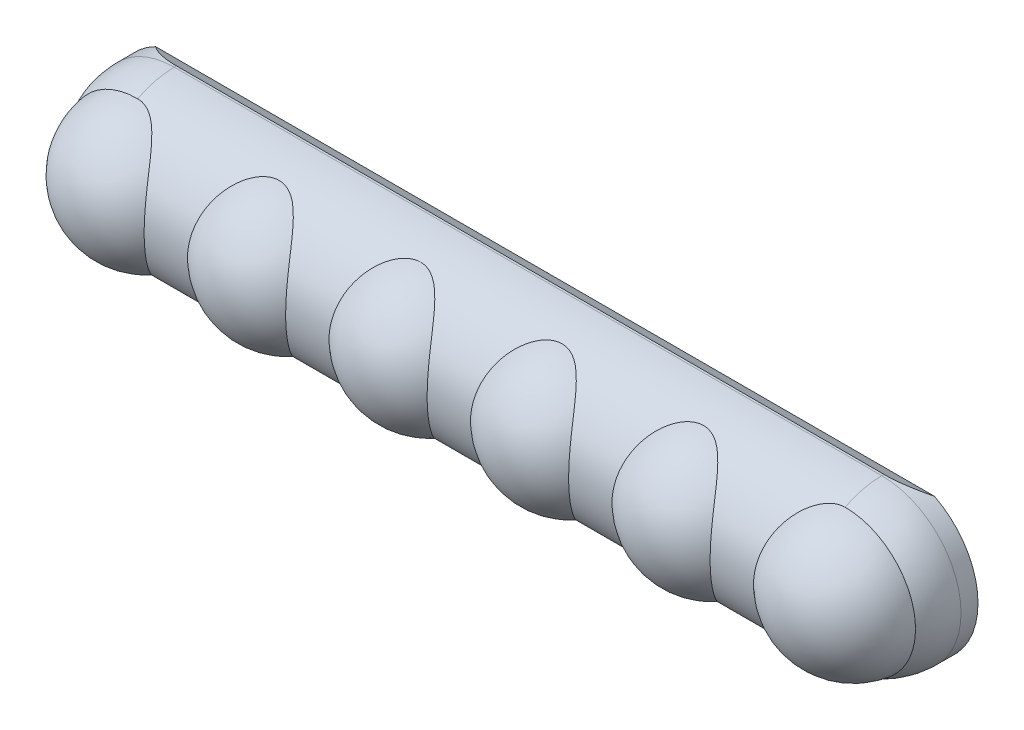
SolidWorks part; units mm, degrees
ref_plane "Front Plane" through (0, 0, 0) normal (0, 0, 1) x (1, 0, 0)
ref_plane "Top Plane" through (0, 0, 0) normal (0, 1, 0) x (1, 0, 0)
ref_plane "Right Plane" through (0, 0, 0) normal (1, 0, 0) x (0, 0, -1)
sketch "Sketch1" plane through (0, 0, 0) normal (0, 0, 1) x (1, 0, 0)
  line L0 (62.5, 14) -> (-62.5, 14)
  line L1 (-76.5, 0) -> (76.5, 0)
  line L2 (-76.5, 0) -> (88.9654, 0) construction
  arc A0 (-62.5, 14) -> (-76.5, 0) centre (-62.5, 0) ccw
  arc A1 (76.5, 0) -> (62.5, 14) centre (62.5, 0) ccw
  dimension "D2" = 14
  dimension "D1" = 125
revolve "Revolve1" add sketch "Sketch1" angle 180 about L2
ref_plane "Plane1" through (0, 0, 5) normal (0, 0, 1) x (1, 0, 0)
sketch "Sketch3" plane through (0, 0, 5) normal (0, 0, 1) x (1, 0, 0)
  line L0 (-62.5, -14) -> (-62.5, 14) construction
  line L1 (-75, 0) -> (-50, 0)
  line L2 (-75, 0) -> (-41.585, 0) construction
  arc A0 (-50, 0) -> (-75, 0) centre (-62.5, 0) ccw
  dimension "D1" = 25
revolve "Revolve2" add sketch "Sketch3" angle 180 about L2
pattern_linear "LPattern1" count 6 spacing 25 along (1, 0, 0) of "Revolve2"
sketch "Sketch4" plane through (0, 0, 0) normal (0, 0, -1) x (-1, 0, 0)
  line L2 (-62.5, -14) -> (62.5, -14)
  line L3 (62.5, 14) -> (-62.5, 14)
  line L4 (-62.5, -14) -> (62.5, -14)
  line L5 (62.5, 14) -> (-62.5, 14)
  arc A2 (-62.5, 14) -> (-62.5, -14) centre (-62.5, 0) ccw
  arc A3 (62.5, -14) -> (62.5, 14) centre (62.5, 0) ccw
  arc A4 (-62.5, 14) -> (-62.5, -14) centre (-62.5, 0) ccw
  arc A5 (62.5, -14) -> (62.5, 14) centre (62.5, 0) ccw
  dimension "D1" = 0
extrude "Boss-Extrude1" add sketch "Sketch4" along normal blind 3
sketch "Sketch5" plane through (0, 0, 0) normal (1, 0, 0) x (0, 0, -1)
  line L0 (0.3987, 13.9943) -> (0.3987, 14.6466)
  line L1 (0.3987, 13.9943) -> (3, 12.5)
  line L2 (3, -14) -> (3, 14) construction
  line L3 (3, 12.5) -> (3, 14.6466)
  line L4 (3, -14) -> (0.3987, -14)
  line L5 (0.3987, -14) -> (3, -12.5)
  line L6 (3, -12.5) -> (3, -14)
  line L7 (0.3987, 14.6466) -> (3, 14.6466)
  arc A0 (0, 14) -> (-6.475, 12.4127) centre (0, 0) ccw construction
  dimension "D1" = 29.875
  dimension "D2" = 12.5
  dimension "D3" = 0.6523
  dimension "D4" = 29.969
extrude "Cut-Extrude4" cut sketch "Sketch5" against normal through all and the other way through all
sketch "Sketch6" plane through (0, 0, -3) normal (0, 0, -1) x (-1, 0, 0)
  circle A0 centre (0, 0) radius 2.6
  circle A1 centre (62.5, 0) radius 2.6
  circle A2 centre (-62.5, 0) radius 2.6
  dimension "D1" = 5.2
extrude "Cut-Extrude5" cut sketch "Sketch6" against normal blind 8
sketch "Sketch7" plane through (0, 0, -3) normal (0, 0, -1) x (-1, 0, 0)
  line L0 (0, 0) -> (-8, 0) construction
  line L1 (-54.5, 6) -> (-8, 6)
  line L2 (-54.5, 6) -> (-54.5, -6)
  line L3 (-54.5, -6) -> (-8, -6)
  line L4 (-8, 6) -> (-8, -6)
  line L5 (8, 6) -> (54.5, 6)
  line L6 (8, 6) -> (8, -6)
  line L7 (8, -6) -> (54.5, -6)
  line L8 (54.5, 6) -> (54.5, -6)
  line L9 (0, 0) -> (8, 0) construction
  line L10 (54.5, 0) -> (62.5, 0) construction
  dimension "D1" = 8
  dimension "D2" = 12
extrude "Cut-Extrude6" cut sketch "Sketch7" against normal blind 8
